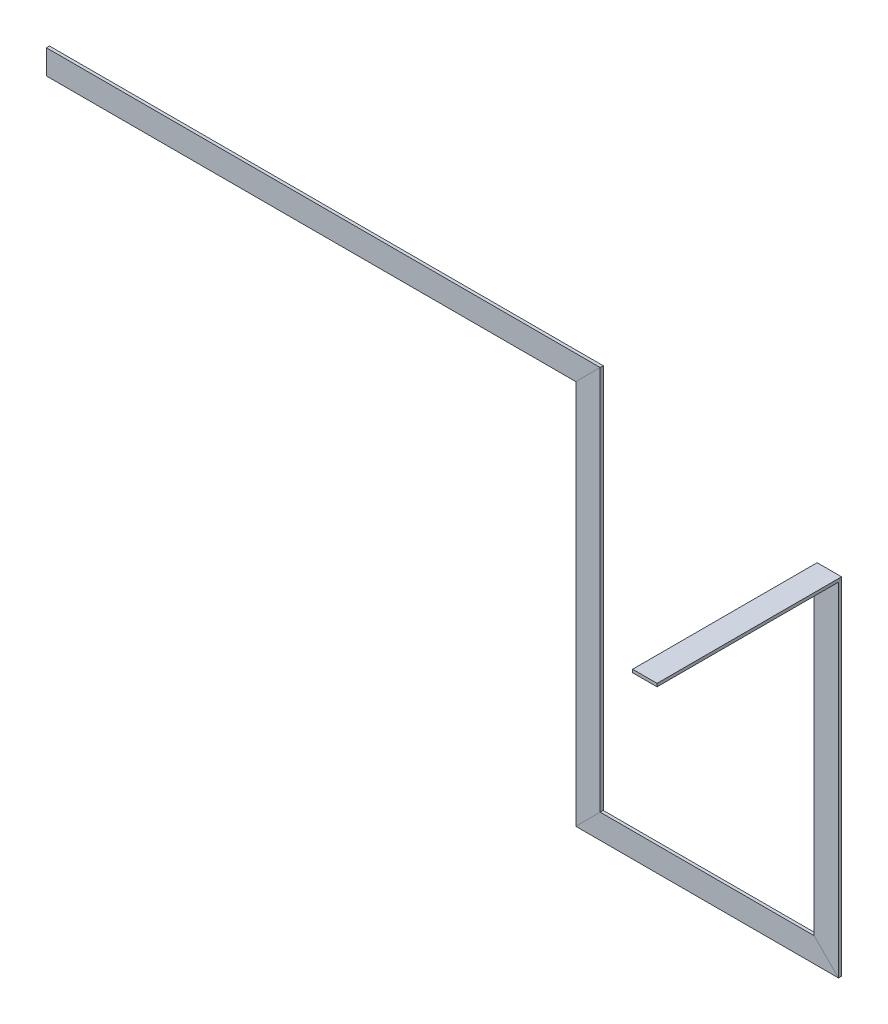
SolidWorks part; units mm, degrees
ref_plane "Alzado" through (0, 0, 0) normal (0, 0, 1) x (1, 0, 0)
ref_plane "Planta" through (0, 0, 0) normal (0, 1, 0) x (1, 0, 0)
ref_plane "Vista lateral" through (0, 0, 0) normal (1, 0, 0) x (0, 0, -1)
sketch3d "Croquis3D2"
  line L0 (709.9375, 181.9091, -50.1818) -> (709.9375, 181.9091, 50.1818)
  line L1 (709.9375, 181.9091, 50.1818) -> (709.9375, -508.0909, 50.1818)
  line L2 (709.9375, -508.0909, 50.1818) -> (214.9366, -508.0909, 50.1818)
  line L3 (214.9366, -508.0909, 50.1818) -> (214.9366, 291.9072, 50.1818)
  line L4 (214.9366, 291.9072, 50.1818) -> (-910.0526, 291.9072, 50.1818)
  dimension "D1" = 690
  dimension "D2" = 495.0009
  dimension "D3" = 799.9981
  dimension "D4" = 1124.9892
sketch "Croquis1" plane through (0, 0, 0) normal (0, 0, 1) x (1, 0, 0)
  line L1 (735.3375, 185.0841) -> (684.5375, 185.0841)
  line L2 (735.3375, 185.0841) -> (735.3375, 178.7341)
  line L3 (735.3375, 178.7341) -> (684.5375, 178.7341)
  line L4 (684.5375, 185.0841) -> (684.5375, 178.7341)
  line L5 (735.3375, 185.0841) -> (684.5375, 178.7341) construction
  line L6 (735.3375, 178.7341) -> (684.5375, 185.0841) construction
  point P0 (709.9375, 181.9091)
  dimension "D1" = 50.8
  dimension "D2" = 6.35
sweep "Barrer1" add profiles "Croquis1" path "Croquis3D2"
ref_plane "Plano1" through (709.9375, 0, 0) normal (1, 0, 0) x (0, 0, -1)
sketch "Croquis2" plane through (0, 0, 0) normal (0, 0, -1) x (-1, 0, 0)
  line L0 (-735.3375, 185.0841) -> (-684.5375, 185.0841)
  line L1 (-684.5375, 185.0841) -> (-684.5375, 178.7341)
  line L2 (-684.5375, 178.7341) -> (-735.3375, 178.7341)
  line L3 (-735.3375, 178.7341) -> (-735.3375, 185.0841)
extrude "Saliente-Extruir1" add sketch "Croquis2" along normal blind 34.82
sketch "Croquis3" plane through (0, 0, 53.3568) normal (0, 0, 1) x (1, 0, 0)
  line L0 (684.5375, 185.0841) -> (684.5375, 178.7341)
  line L1 (684.5375, 178.7341) -> (735.3375, 178.7341)
  line L2 (735.3375, 178.7341) -> (735.3375, 185.0841)
  line L3 (735.3375, 185.0841) -> (684.5375, 185.0841)
extrude "Saliente-Extruir2" add sketch "Croquis3" along normal blind 377
sketch "Croquis4" plane through (0, 185.0841, 0) normal (0, 1, 0) x (1, 0, 0)
  line L0 (684.5375, 34.82) -> (735.3375, 34.82)
  line L1 (735.3375, 34.82) -> (735.3375, -47.0068)
  line L2 (735.3375, 34.82) -> (735.3375, -53.3568) construction
  line L3 (735.3375, -47.0068) -> (684.5375, -47.0068)
  line L4 (684.5375, -47.0068) -> (684.5375, 34.82)
extrude "Cortar-Extruir1" cut sketch "Croquis4" against normal blind 29
